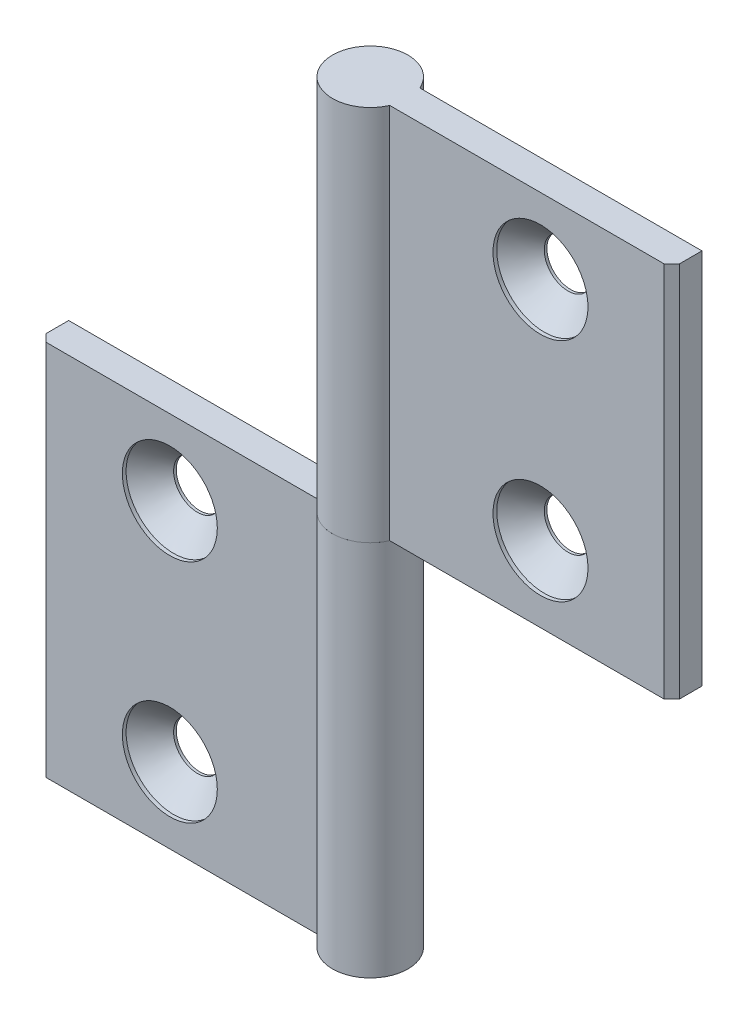
SolidWorks part; units mm, degrees
material "Алюминиевый сплав"
ref_plane "Спереди" through (0, 0, 0) normal (0, 0, 1) x (1, 0, 0)
ref_plane "Сверху" through (0, 0, 0) normal (0, 1, 0) x (1, 0, 0)
ref_plane "Справа" through (0, 0, 0) normal (1, 0, 0) x (0, 0, -1)
sketch "Эскиз1" plane through (0, 0, 0) normal (0, 1, 0) x (1, 0, 0)
  line L0 (-4.5826, 2) -> (-42, 2)
  line L1 (-42, 2) -> (-42, -1)
  line L2 (-42, -1) -> (-41, -2)
  line L3 (-41, -2) -> (-4.5826, -2)
  line L5 (-23.2913, 2) -> (-23.2913, -2) construction
  arc A0 (-4.5826, -2) -> (-4.5826, 2) centre (0, 0) ccw
  point P1 (-23.2913, 0)
  dimension "D5" = 5
  dimension "D1" = 37
  dimension "D2" = 4
  dimension "D3" = 3
  dimension "D4" = 45
extrude "Бобышка-Вытянуть1" add sketch "Эскиз1" along normal mid plane 50
hole_wizard "Зенковка для винта с полупотайной головкой M61" positions "Эскиз4" profile "Эскиз6" countersink size "M6" standard "ISO" end condition through all
sketch "Эскиз4" plane through (0, 0, 2) normal (0, 0, 1) x (1, 0, 0)
  line L0 (-24.5826, 15) -> (-24.5826, -15)
  line L2 (0.2087, -18.4577) -> (0.2087, 25) construction
  line L4 (5, 25) -> (-4.5826, 25) construction
  line L5 (-4.5826, 25) -> (-4.5826, -25) construction
  point P0 (-24.5826, 15)
  point P2 (-24.5826, -15)
  point P9 (-24.5826, 0)
  dimension "D1" = 30
  dimension "D2" = 20
sketch "Эскиз6" plane through (-24.5826, 15, 2) normal (1, 0, 0) x (0, -1, 0)
  line L0 (0, 0) -> (0, 7)
  line L1 (0, 7) -> (3.15, 7)
  line L2 (3.15, 7) -> (3.15, 3.65)
  line L3 (3.15, 3.65) -> (6.3, 0.5)
  line L4 (6.3, 0.5) -> (6.3, 0)
  line L6 (6.3, 0) -> (0, 0)
  line L7 (-3.15, 3.65) -> (-6.3, 0.5) construction
  line L11 (0, -6.35) -> (0, 107.95) construction
  dimension "Диаметр сквозного отверстия" = 6.3
  dimension "Глубина сквозного отверстия" = 7
  dimension "Диаметр зенковки" = 12.6
  dimension "Угол зенковки" = 90
  dimension "Утопленность" = 0.5
sketch "Угол раскрытия" plane through (0, 25, 0) normal (0, 1, 0) x (1, 0, 0)
  line L0 (0, 0) -> (0, -10)
  line L7 (-4.5826, 2) -> (-42, 2) construction
  dimension "D1" = 10
  dimension "D2" = 90
pattern_circular "Круговой массив1" count 2 over 360 about axis through (0, 25, 0) along (0, 0, 1) of bodies 106
